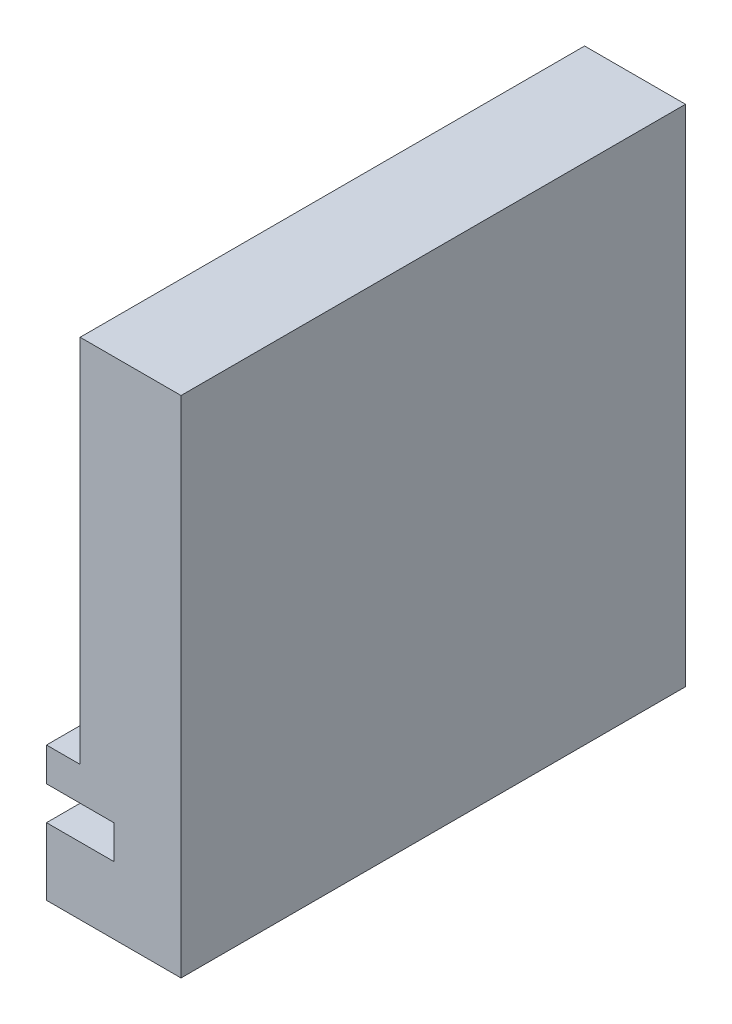
SolidWorks part; units mm, degrees
ref_plane "Front Plane" through (0, 0, 0) normal (0, 0, 1) x (1, 0, 0)
ref_plane "Top Plane" through (0, 0, 0) normal (0, 1, 0) x (1, 0, 0)
ref_plane "Right Plane" through (0, 0, 0) normal (1, 0, 0) x (0, 0, -1)
sketch "Sketch1" plane through (0, 0, 0) normal (0, 0, 1) x (1, 0, 0)
  line L2 (40, 150) -> (10, 150)
  line L14 (10, 150) -> (10, 40)
  line L15 (0, 40) -> (0, 30)
  line L16 (0, 30) -> (20, 30)
  line L17 (20, 30) -> (20, 20)
  line L18 (20, 20) -> (0, 20)
  line L19 (0, 20) -> (0, 0)
  line L20 (55, 0) -> (-55, 0) construction
  line L21 (0, 0) -> (40, 0)
  line L22 (40, 0) -> (40, 150)
  line L23 (0, 40) -> (10, 40)
  point P6 (42.1673, 85.1548)
  dimension "D1" = 40
  dimension "D2" = 20
  dimension "D3" = 10
  dimension "D4" = 20
  dimension "D5" = 10
  dimension "D6" = 30
  dimension "D7" = 150
extrude "Boss-Extrude1" add sketch "Sketch1" along normal blind 150
